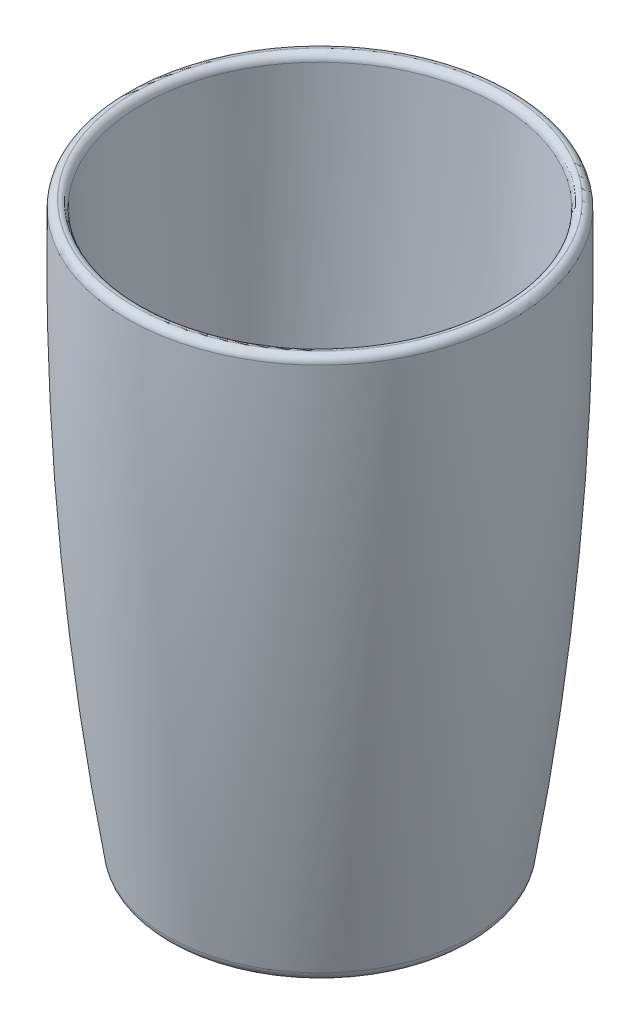
SolidWorks part; units mm, degrees
ref_plane "Front Plane" through (0, 0, 0) normal (0, 0, 1) x (1, 0, 0)
ref_plane "Top Plane" through (0, 0, 0) normal (0, 1, 0) x (1, 0, 0)
ref_plane "Right Plane" through (0, 0, 0) normal (1, 0, 0) x (0, 0, -1)
sketch "Sketch1" plane through (0, 0, 0) normal (0, 0, 1) x (1, 0, 0)
  line L0 (-103.1946, -2.149) -> (-71.3491, -2.149)
  line L1 (-97.1479, 1.026) -> (-103.1946, 1.026)
  line L2 (-62.5546, 118.4129) -> (-65.6026, 118.4129)
  line L3 (-103.1946, -2.149) -> (-103.1946, 1.026)
  arc A0 (-71.3491, -2.149) -> (-62.5546, 118.4129) centre (-748.443, 107.844) ccw
  spline S0 degree 9 poles (-100.3229, 1.0204) (-96.3988, 1.0273) (-92.4747, 1.0341) (-88.5506, 1.0411) (-84.6265, 1.0466) (-80.7024, 1.0672) (-76.7781, 0.9352) (-72.8565, 2.3469) (-68.9076, -11.8678) (-65.2347, 132.1093) knots 0 0 0 0 0 0 0 0 0 0 1 1 1 1 1 1 1 1 1 1 construction
  spline S1 degree 9 poles (-97.1479, 1.026) (-93.6201, 1.0321) (-90.0923, 1.0383) (-86.5646, 1.0444) (-83.0368, 1.0506) (-79.509, 1.0568) (-75.9813, 1.0629) (-72.4535, 1.0691) (-68.9257, 1.0752) (-65.6026, 118.4129) knots 0.0899 0.0899 0.0899 0.0899 0.0899 0.0899 0.0899 0.0899 0.0899 0.0899 0.988904 0.988904 0.988904 0.988904 0.988904 0.988904 0.988904 0.988904 0.988904 0.988904
  dimension "D1" = 40.64
  dimension "D2" = 3.048
  dimension "D3" = 3.175
revolve "Revolve2" add sketch "Sketch1" angle 360 about L3
fillet "Fillet2" radius 2.54 1 edges at (-103.1946, -2.149, -31.8455)
fillet "Fillet8" radius 1.524 2 edges at (-103.1946, 118.4129, -37.592) (-103.1946, 118.4129, -40.64)
